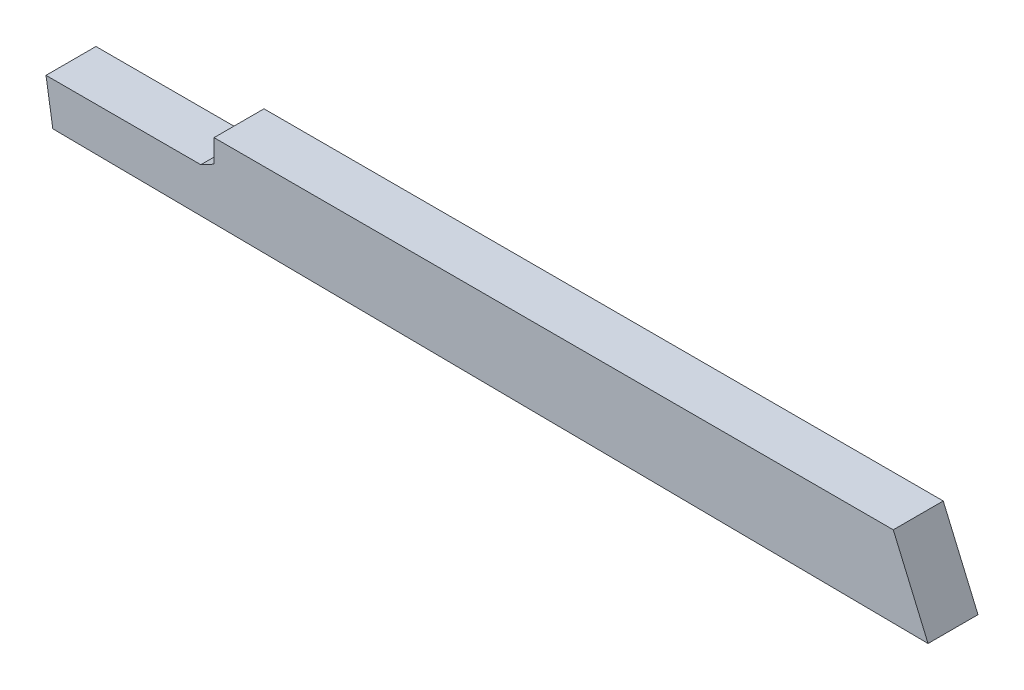
SolidWorks part; units mm, degrees
ref_plane "Front Plane" through (0, 0, 0) normal (0, 0, 1) x (1, 0, 0)
ref_plane "Top Plane" through (0, 0, 0) normal (0, 1, 0) x (1, 0, 0)
ref_plane "Right Plane" through (0, 0, 0) normal (1, 0, 0) x (0, 0, -1)
sketch "Sketch1" plane through (0, 0, 0) normal (0, 0, 1) x (1, 0, 0)
  line L0 (0, 0) -> (34.544, 0)
  line L1 (34.544, 0) -> (36.3123, -4.1249)
  line L2 (0, 0) -> (0, -1.1684)
  line L3 (0, -1.1684) -> (-0.6717, -1.5282)
  line L4 (-0.6717, -1.5282) -> (-8.5457, -1.5282)
  line L5 (-8.5457, -1.5282) -> (-8.1996, -3.7107)
  line L6 (-8.1996, -3.7107) -> (36.3123, -4.1249)
  dimension "D1" = 2.2098
  dimension "D2" = 7.874
  dimension "D3" = 0.762
  dimension "D4" = 34.544
  dimension "D5" = 80.989
  dimension "D6" = 208.175
  dimension "D7" = 113.204
  dimension "D8" = 1.1684
extrude "Boss-Extrude1" add sketch "Sketch1" along normal blind 2.54
